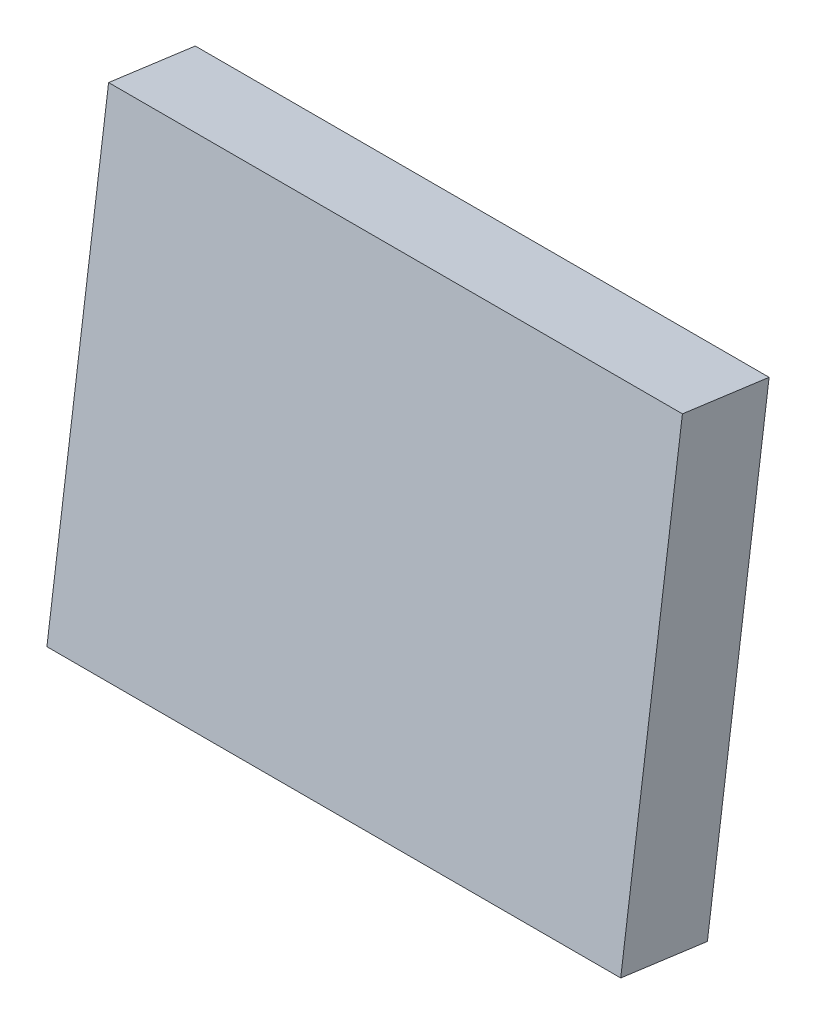
SolidWorks part; units mm, degrees
ref_plane "Front Plane" through (0, 0, 0) normal (0, 0, 1) x (1, 0, 0)
ref_plane "Top Plane" through (0, 0, 0) normal (0, 1, 0) x (1, 0, 0)
ref_plane "Right Plane" through (0, 0, 0) normal (1, 0, 0) x (0, 0, -1)
sketch "Sketch2" plane through (0, -126.5651, -938.8101) normal (0, -0.1336, -0.991) x (1, 0, 0)
  line L0 (-68.5919, -1.0242) -> (-68.5919, 25.3758)
  line L1 (-68.5919, -1.0242) -> (-35.7919, -1.0242)
  line L2 (-68.5919, 25.3758) -> (-35.7919, 25.3758)
  line L3 (-35.7919, -1.0242) -> (-35.7919, 25.3758)
extrude "Boss-Extrude1" add sketch "Sketch2" along normal blind 5
sketch "Sketch3" plane through (0, -127.2332, -943.7653) normal (0, -0.1336, -0.991) x (1, 0, 0)
  circle A0 centre (-56.7919, -123.2214) radius 2
  circle A1 centre (-56.7919, -107.7214) radius 2
  circle A2 centre (-42.7919, -123.2214) radius 2
  circle A3 centre (-42.7919, -107.7214) radius 2
  circle A4 centre (-56.7919, -107.7214) radius 2 construction
  circle A5 centre (-42.7919, -107.7214) radius 2 construction
  circle A6 centre (-42.7919, -123.2214) radius 2 construction
  circle A7 centre (-56.7919, -123.2214) radius 2 construction
extrude "Cut-Extrude1" cut sketch "Sketch3" against normal blind 5
